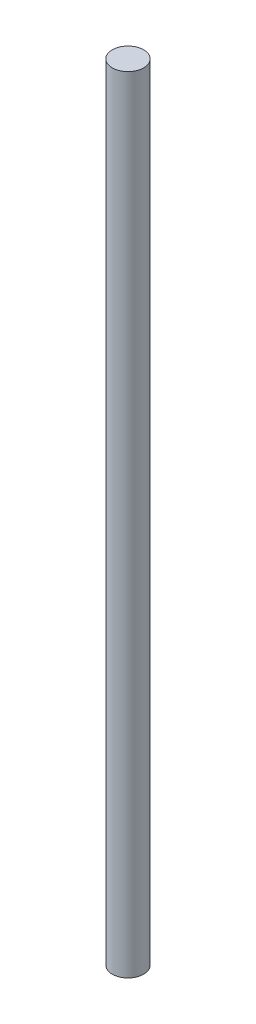
SolidWorks part; units mm, degrees
material "Cast Carbon Steel"
ref_plane "Front Plane" through (0, 0, 0) normal (0, 0, 1) x (1, 0, 0)
ref_plane "Top Plane" through (0, 0, 0) normal (0, 1, 0) x (1, 0, 0)
ref_plane "Right Plane" through (0, 0, 0) normal (1, 0, 0) x (0, 0, -1)
sketch "Sketch1" plane through (0, 0, 0) normal (0, 1, 0) x (1, 0, 0)
  circle A0 centre (0, 0) radius 4
  dimension "D1" = 8
extrude "Boss-Extrude1" add sketch "Sketch1" along normal blind 200
sketch "Sketch2" plane through (0, 0, 0) normal (0, -1, 0) x (-1, 0, 0)
  circle A0 centre (0, 0) radius 3
  dimension "D1" = 6
